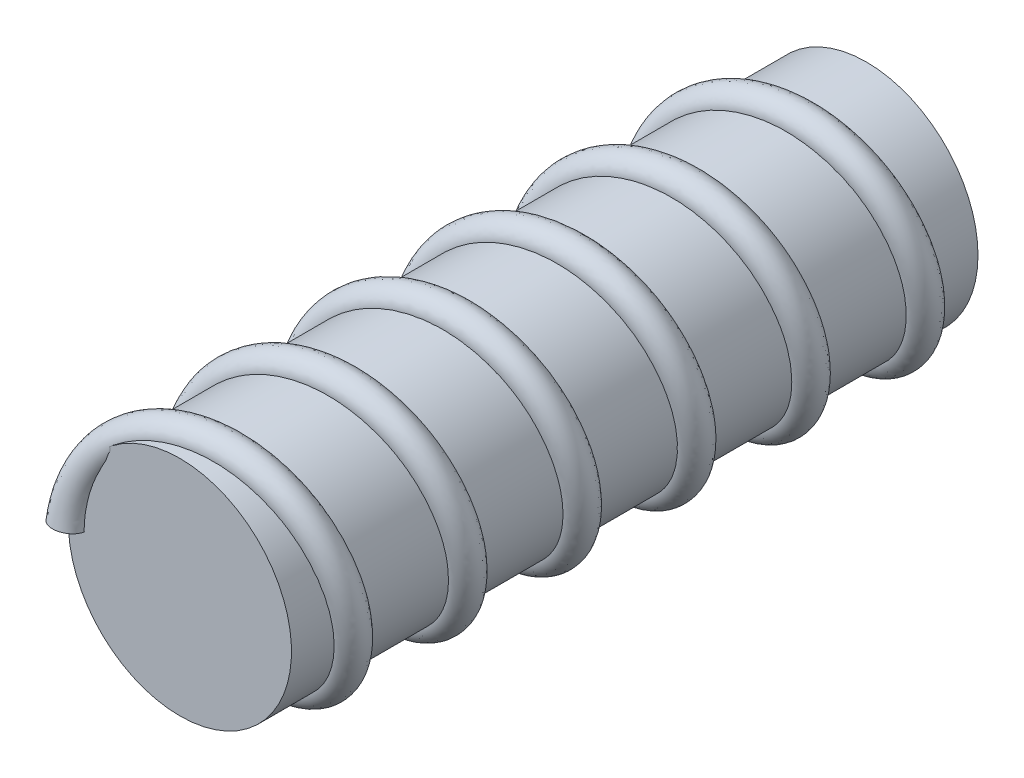
SolidWorks part; units mm, degrees
ref_plane "Front Plane" through (0, 0, 0) normal (0, 0, 1) x (1, 0, 0)
ref_plane "Top Plane" through (0, 0, 0) normal (0, 1, 0) x (1, 0, 0)
ref_plane "Right Plane" through (0, 0, 0) normal (1, 0, 0) x (0, 0, -1)
ref_plane "Plane1" through (0, 0, 0) normal (0, 0, 1) x (1, 0, 0)
ref_plane "Plane2" through (0, 0, 129.2399) normal (0, 0, -1) x (-1, 0, 0)
sketch "Sketch2" plane through (0, 0, 0) normal (0, 0, 1) x (1, 0, 0)
  circle A0 centre (0, 0) radius 21
  dimension "D1" = 42
extrude "Boss-Extrude2" add sketch "Sketch2" along normal up to surface (129.2399 mm away) contours A0 up to plane "Plane2"
sketch "Sketch3" plane through (0, 0, 0) normal (0, 0, 1) x (1, 0, 0)
  line L0 (0, 0) -> (-21, 0)
  circle A0 centre (0, 0) radius 21 construction
sketch "Sketch9" plane through (0, 0, 129.2399) normal (0, 0, -1) x (-1, 0, 0)
  point P0 (0, 0)
sketch "Sketch10" plane through (0, 0, 0) normal (0, 1, 0) x (1, 0, 0)
  line L0 (0, 0) -> (0, -129.2399)
surface "Surface-Sweep1" parameters "D0"=2160
sketch3d "3DSketch1"
  spline S0 degree 2 poles (-21, 0, 129.2399) (-21, 6.8233, 128.1629) (-16.9894, 12.3435, 127.0859) (-12.9787, 17.8637, 126.0089) (-6.4894, 19.9722, 124.9319) (0, 22.0807, 123.8549) (6.4894, 19.9722, 122.7779) (12.9787, 17.8637, 121.7009) (16.9894, 12.3435, 120.6239) (21, 6.8233, 119.5469) (21, 0, 118.4699) (21, -6.8233, 117.3929) (16.9894, -12.3435, 116.3159) (12.9787, -17.8637, 115.2389) (6.4894, -19.9722, 114.1619) (0, -22.0807, 113.0849) (-6.4894, -19.9722, 112.0079) (-12.9787, -17.8637, 110.9309) (-16.9894, -12.3435, 109.8539) (-21, -6.8233, 108.7769) (-21, 0, 107.6999) (-21, 6.8233, 106.6229) (-16.9894, 12.3435, 105.5459) (-12.9787, 17.8637, 104.4689) (-6.4894, 19.9722, 103.3919) (0, 22.0807, 102.3149) (6.4894, 19.9722, 101.2379) (12.9787, 17.8637, 100.1609) (16.9894, 12.3435, 99.0839) (21, 6.8233, 98.0069) (21, 0, 96.9299) (21, -6.8233, 95.8529) (16.9894, -12.3435, 94.7759) (12.9787, -17.8637, 93.6989) (6.4894, -19.9722, 92.6219) (0, -22.0807, 91.5449) (-6.4894, -19.9722, 90.4679) (-12.9787, -17.8637, 89.3909) (-16.9894, -12.3435, 88.3139) (-21, -6.8233, 87.2369) (-21, 0, 86.1599) (-21, 6.8233, 85.0829) (-16.9894, 12.3435, 84.0059) (-12.9787, 17.8637, 82.9289) (-6.4894, 19.9722, 81.8519) (0, 22.0807, 80.7749) (6.4894, 19.9722, 79.6979) (12.9787, 17.8637, 78.6209) (16.9894, 12.3435, 77.5439) (21, 6.8233, 76.4669) (21, 0, 75.3899) (21, -6.8233, 74.3129) (16.9894, -12.3435, 73.2359) (12.9787, -17.8637, 72.1589) (6.4894, -19.9722, 71.0819) (0, -22.0807, 70.0049) (-6.4894, -19.9722, 68.928) (-12.9787, -17.8637, 67.851) (-16.9894, -12.3435, 66.774) (-21, -6.8233, 65.697) (-21, 0, 64.62) (-21, 6.8233, 63.543) (-16.9894, 12.3435, 62.466) (-12.9787, 17.8637, 61.389) (-6.4894, 19.9722, 60.312) (0, 22.0807, 59.235) (6.4894, 19.9722, 58.158) (12.9787, 17.8637, 57.081) (16.9894, 12.3435, 56.004) (21, 6.8233, 54.927) (21, 0, 53.85) (21, -6.8233, 52.773) (16.9894, -12.3435, 51.696) (12.9787, -17.8637, 50.619) (6.4894, -19.9722, 49.542) (0, -22.0807, 48.465) (-6.4894, -19.9722, 47.388) (-12.9787, -17.8637, 46.311) (-16.9894, -12.3435, 45.234) (-21, -6.8233, 44.157) (-21, 0, 43.08) (-21, 6.8233, 42.003) (-16.9894, 12.3435, 40.926) (-12.9787, 17.8637, 39.849) (-6.4894, 19.9722, 38.772) (0, 22.0807, 37.695) (6.4894, 19.9722, 36.618) (12.9787, 17.8637, 35.541) (16.9894, 12.3435, 34.464) (21, 6.8233, 33.387) (21, 0, 32.31) (21, -6.8233, 31.233) (16.9894, -12.3435, 30.156) (12.9787, -17.8637, 29.079) (6.4894, -19.9722, 28.002) (0, -22.0807, 26.925) (-6.4894, -19.9722, 25.848) (-12.9787, -17.8637, 24.771) (-16.9894, -12.3435, 23.694) (-21, -6.8233, 22.617) (-21, 0, 21.54) (-21, 6.8233, 20.463) (-16.9894, 12.3435, 19.386) (-12.9787, 17.8637, 18.309) (-6.4894, 19.9722, 17.232) (0, 22.0807, 16.155) (6.4894, 19.9722, 15.078) (12.9787, 17.8637, 14.001) (16.9894, 12.3435, 12.924) (21, 6.8233, 11.847) (21, 0, 10.77) (21, -6.8233, 9.693) (16.9894, -12.3435, 8.616) (12.9787, -17.8637, 7.539) (6.4894, -19.9722, 6.462) (0, -22.0807, 5.385) (-6.4894, -19.9722, 4.308) (-12.9787, -17.8637, 3.231) (-16.9894, -12.3435, 2.154) (-21, -6.8233, 1.077) (-21, 0, 0) knots 0 0 0 0.016667 0.016667 0.033333 0.033333 0.05 0.05 0.066667 0.066667 0.083333 0.083333 0.1 0.1 0.116667 0.116667 0.133333 0.133333 0.15 0.15 0.166667 0.166667 0.183333 0.183333 0.2 0.2 0.216667 0.216667 0.233333 0.233333 0.25 0.25 0.266667 0.266667 0.283333 0.283333 0.3 0.3 0.316667 0.316667 0.333333 0.333333 0.35 0.35 0.366667 0.366667 0.383333 0.383333 0.4 0.4 0.416667 0.416667 0.433333 0.433333 0.45 0.45 0.466667 0.466667 0.483333 0.483333 0.5 0.5 0.516667 0.516667 0.533333 0.533333 0.55 0.55 0.566667 0.566667 0.583333 0.583333 0.6 0.6 0.616667 0.616667 0.633333 0.633333 0.65 0.65 0.666667 0.666667 0.683333 0.683333 0.7 0.7 0.716667 0.716667 0.733333 0.733333 0.75 0.75 0.766667 0.766667 0.783333 0.783333 0.8 0.8 0.816667 0.816667 0.833333 0.833333 0.85 0.85 0.866667 0.866667 0.883333 0.883333 0.9 0.9 0.916667 0.916667 0.933333 0.933333 0.95 0.95 0.966667 0.966667 0.983333 0.983333 1 1 1 weights 1 0.951057 1 0.951057 1 0.951057 1 0.951057 1 0.951057 1 0.951057 1 0.951057 1 0.951057 1 0.951057 1 0.951057 1 0.951057 1 0.951057 1 0.951057 1 0.951057 1 0.951057 1 0.951057 1 0.951057 1 0.951057 1 0.951057 1 0.951057 1 0.951057 1 0.951057 1 0.951057 1 0.951057 1 0.951057 1 0.951057 1 0.951057 1 0.951057 1 0.951057 1 0.951057 1 0.951057 1 0.951057 1 0.951057 1 0.951057 1 0.951057 1 0.951057 1 0.951057 1 0.951057 1 0.951057 1 0.951057 1 0.951057 1 0.951057 1 0.951057 1 0.951057 1 0.951057 1 0.951057 1 0.951057 1 0.951057 1 0.951057 1 0.951057 1 0.951057 1 0.951057 1 0.951057 1 0.951057 1 0.951057 1 0.951057 1 0.951057 1 0.951057 1 0.951057 1 0.951057 1
  spline S1 degree 2 poles (-21, 0, 129.2399) (-21, 6.8233, 128.1629) (-16.9894, 12.3435, 127.0859) (-12.9787, 17.8637, 126.0089) (-6.4894, 19.9722, 124.9319) (0, 22.0807, 123.8549) (6.4894, 19.9722, 122.7779) (12.9787, 17.8637, 121.7009) (16.9894, 12.3435, 120.6239) (21, 6.8233, 119.5469) (21, 0, 118.4699) (21, -6.8233, 117.3929) (16.9894, -12.3435, 116.3159) (12.9787, -17.8637, 115.2389) (6.4894, -19.9722, 114.1619) (0, -22.0807, 113.0849) (-6.4894, -19.9722, 112.0079) (-12.9787, -17.8637, 110.9309) (-16.9894, -12.3435, 109.8539) (-21, -6.8233, 108.7769) (-21, 0, 107.6999) (-21, 6.8233, 106.6229) (-16.9894, 12.3435, 105.5459) (-12.9787, 17.8637, 104.4689) (-6.4894, 19.9722, 103.3919) (0, 22.0807, 102.3149) (6.4894, 19.9722, 101.2379) (12.9787, 17.8637, 100.1609) (16.9894, 12.3435, 99.0839) (21, 6.8233, 98.0069) (21, 0, 96.9299) (21, -6.8233, 95.8529) (16.9894, -12.3435, 94.7759) (12.9787, -17.8637, 93.6989) (6.4894, -19.9722, 92.6219) (0, -22.0807, 91.5449) (-6.4894, -19.9722, 90.4679) (-12.9787, -17.8637, 89.3909) (-16.9894, -12.3435, 88.3139) (-21, -6.8233, 87.2369) (-21, 0, 86.1599) (-21, 6.8233, 85.0829) (-16.9894, 12.3435, 84.0059) (-12.9787, 17.8637, 82.9289) (-6.4894, 19.9722, 81.8519) (0, 22.0807, 80.7749) (6.4894, 19.9722, 79.6979) (12.9787, 17.8637, 78.6209) (16.9894, 12.3435, 77.5439) (21, 6.8233, 76.4669) (21, 0, 75.3899) (21, -6.8233, 74.3129) (16.9894, -12.3435, 73.2359) (12.9787, -17.8637, 72.1589) (6.4894, -19.9722, 71.0819) (0, -22.0807, 70.0049) (-6.4894, -19.9722, 68.928) (-12.9787, -17.8637, 67.851) (-16.9894, -12.3435, 66.774) (-21, -6.8233, 65.697) (-21, 0, 64.62) (-21, 6.8233, 63.543) (-16.9894, 12.3435, 62.466) (-12.9787, 17.8637, 61.389) (-6.4894, 19.9722, 60.312) (0, 22.0807, 59.235) (6.4894, 19.9722, 58.158) (12.9787, 17.8637, 57.081) (16.9894, 12.3435, 56.004) (21, 6.8233, 54.927) (21, 0, 53.85) (21, -6.8233, 52.773) (16.9894, -12.3435, 51.696) (12.9787, -17.8637, 50.619) (6.4894, -19.9722, 49.542) (0, -22.0807, 48.465) (-6.4894, -19.9722, 47.388) (-12.9787, -17.8637, 46.311) (-16.9894, -12.3435, 45.234) (-21, -6.8233, 44.157) (-21, 0, 43.08) (-21, 6.8233, 42.003) (-16.9894, 12.3435, 40.926) (-12.9787, 17.8637, 39.849) (-6.4894, 19.9722, 38.772) (0, 22.0807, 37.695) (6.4894, 19.9722, 36.618) (12.9787, 17.8637, 35.541) (16.9894, 12.3435, 34.464) (21, 6.8233, 33.387) (21, 0, 32.31) (21, -6.8233, 31.233) (16.9894, -12.3435, 30.156) (12.9787, -17.8637, 29.079) (6.4894, -19.9722, 28.002) (0, -22.0807, 26.925) (-6.4894, -19.9722, 25.848) (-12.9787, -17.8637, 24.771) (-16.9894, -12.3435, 23.694) (-21, -6.8233, 22.617) (-21, 0, 21.54) (-21, 6.8233, 20.463) (-16.9894, 12.3435, 19.386) (-12.9787, 17.8637, 18.309) (-6.4894, 19.9722, 17.232) (0, 22.0807, 16.155) (6.4894, 19.9722, 15.078) (12.9787, 17.8637, 14.001) (16.9894, 12.3435, 12.924) (21, 6.8233, 11.847) (21, 0, 10.77) (21, -6.8233, 9.693) (16.9894, -12.3435, 8.616) (12.9787, -17.8637, 7.539) (6.4894, -19.9722, 6.462) (0, -22.0807, 5.385) (-6.4894, -19.9722, 4.308) (-12.9787, -17.8637, 3.231) (-16.9894, -12.3435, 2.154) (-21, -6.8233, 1.077) (-21, 0, 0) knots 0 0 0 0.016667 0.016667 0.033333 0.033333 0.05 0.05 0.066667 0.066667 0.083333 0.083333 0.1 0.1 0.116667 0.116667 0.133333 0.133333 0.15 0.15 0.166667 0.166667 0.183333 0.183333 0.2 0.2 0.216667 0.216667 0.233333 0.233333 0.25 0.25 0.266667 0.266667 0.283333 0.283333 0.3 0.3 0.316667 0.316667 0.333333 0.333333 0.35 0.35 0.366667 0.366667 0.383333 0.383333 0.4 0.4 0.416667 0.416667 0.433333 0.433333 0.45 0.45 0.466667 0.466667 0.483333 0.483333 0.5 0.5 0.516667 0.516667 0.533333 0.533333 0.55 0.55 0.566667 0.566667 0.583333 0.583333 0.6 0.6 0.616667 0.616667 0.633333 0.633333 0.65 0.65 0.666667 0.666667 0.683333 0.683333 0.7 0.7 0.716667 0.716667 0.733333 0.733333 0.75 0.75 0.766667 0.766667 0.783333 0.783333 0.8 0.8 0.816667 0.816667 0.833333 0.833333 0.85 0.85 0.866667 0.866667 0.883333 0.883333 0.9 0.9 0.916667 0.916667 0.933333 0.933333 0.95 0.95 0.966667 0.966667 0.983333 0.983333 1 1 1 weights 1 0.951057 1 0.951057 1 0.951057 1 0.951057 1 0.951057 1 0.951057 1 0.951057 1 0.951057 1 0.951057 1 0.951057 1 0.951057 1 0.951057 1 0.951057 1 0.951057 1 0.951057 1 0.951057 1 0.951057 1 0.951057 1 0.951057 1 0.951057 1 0.951057 1 0.951057 1 0.951057 1 0.951057 1 0.951057 1 0.951057 1 0.951057 1 0.951057 1 0.951057 1 0.951057 1 0.951057 1 0.951057 1 0.951057 1 0.951057 1 0.951057 1 0.951057 1 0.951057 1 0.951057 1 0.951057 1 0.951057 1 0.951057 1 0.951057 1 0.951057 1 0.951057 1 0.951057 1 0.951057 1 0.951057 1 0.951057 1 0.951057 1 0.951057 1 0.951057 1 0.951057 1 0.951057 1 0.951057 1 0.951057 1 0.951057 1 0.951057 1 0.951057 1 0.951057 1 0.951057 1
surface "Surface-Sweep2" parameters "D2"=6
